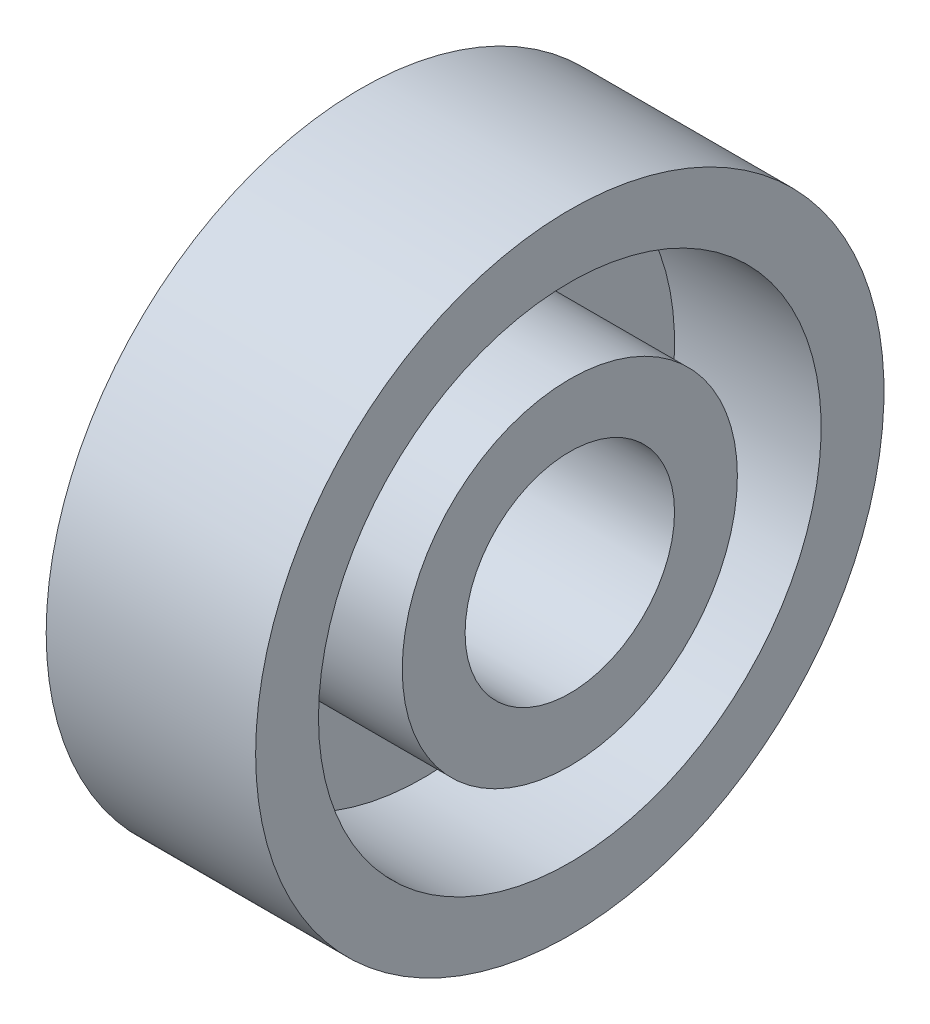
SolidWorks part; units mm, degrees
ref_plane "Ebene vorne" through (0, 0, 0) normal (0, 0, 1) x (1, 0, 0)
ref_plane "Ebene oben" through (0, 0, 0) normal (0, 1, 0) x (1, 0, 0)
ref_plane "Ebene rechts" through (0, 0, 0) normal (1, 0, 0) x (0, 0, -1)
sketch "Skizze1" plane through (0, 0, 0) normal (0, 0, 1) x (1, 0, 0)
  line L0 (0, 0) -> (8.6986, 0) construction
  line L1 (4, 2) -> (0, 2)
  line L2 (0, 2) -> (0, 6)
  line L3 (0, 6) -> (4, 6)
  line L4 (4, 6) -> (4, 4.8)
  line L5 (4, 4.8) -> (1.2, 4.8)
  line L6 (1.2, 4.8) -> (1.2, 3.2)
  line L7 (1.2, 3.2) -> (4, 3.2)
  line L8 (4, 3.2) -> (4, 2)
  dimension "D1" = 4
  dimension "D2" = 12
  dimension "D3" = 4
  dimension "D4" = 1.2
  dimension "D5" = 1.2
  dimension "D6" = 1.2
revolve "Rotation1" add sketch "Skizze1" angle 360 about L0
